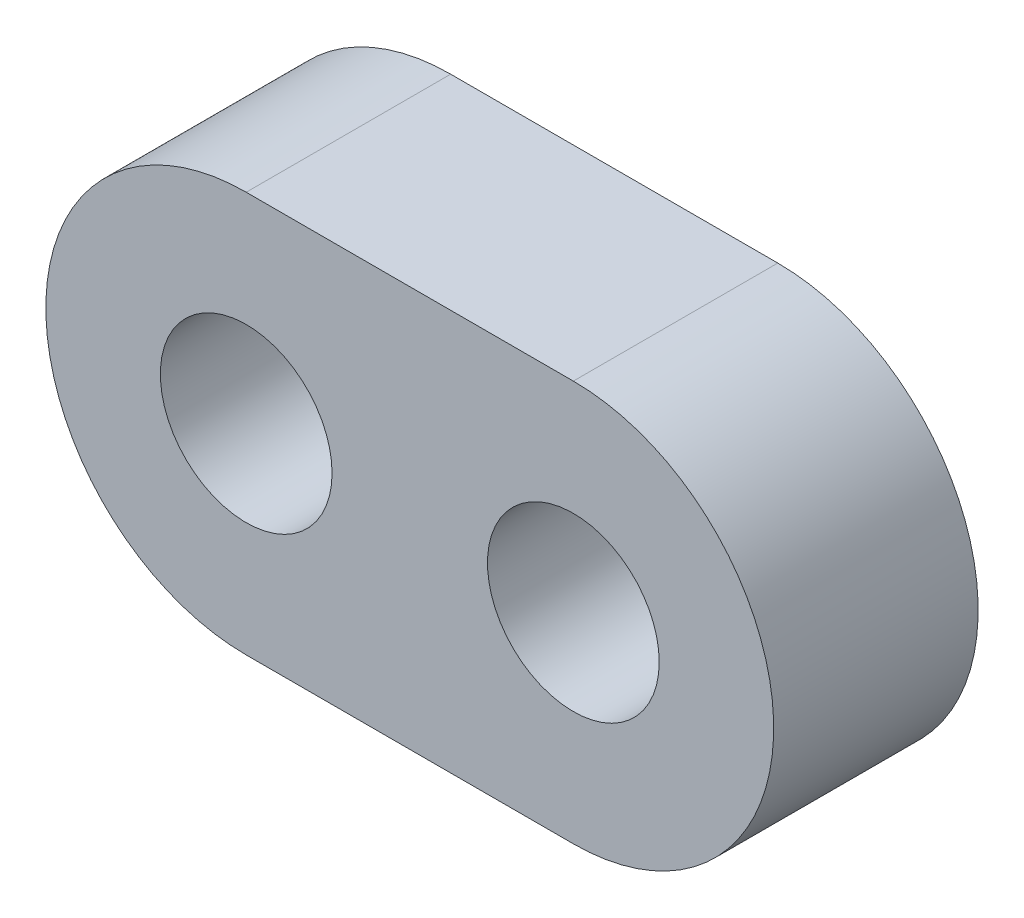
SolidWorks part; units mm, degrees
ref_plane "Front Plane" through (0, 0, 0) normal (0, 0, 1) x (1, 0, 0)
ref_plane "Top Plane" through (0, 0, 0) normal (0, 1, 0) x (1, 0, 0)
ref_plane "Right Plane" through (0, 0, 0) normal (1, 0, 0) x (0, 0, -1)
sketch "Sketch1" plane through (0, 0, 0) normal (0, 0, 1) x (1, 0, 0)
  line L0 (-4, 0) -> (4, 0) construction
  line L1 (-4, 4.9) -> (4, 4.9)
  line L2 (4, -4.9) -> (-4, -4.9)
  circle A0 centre (-4, 0) radius 2.1
  circle A1 centre (4, 0) radius 2.1
  arc A2 (4, 4.9) -> (4, -4.9) centre (4, 0) cw
  arc A3 (-4, -4.9) -> (-4, 4.9) centre (-4, 0) cw
  point P6 (0, 0)
  point P13 (0, 0)
  point P14 (0, 0)
  point P15 (-4, 4.1362)
  dimension "D1" = 4.2
  dimension "D3" = 2.8
  dimension "D2" = 8
extrude "Boss-Extrude1" add sketch "Sketch1" along normal blind 5
